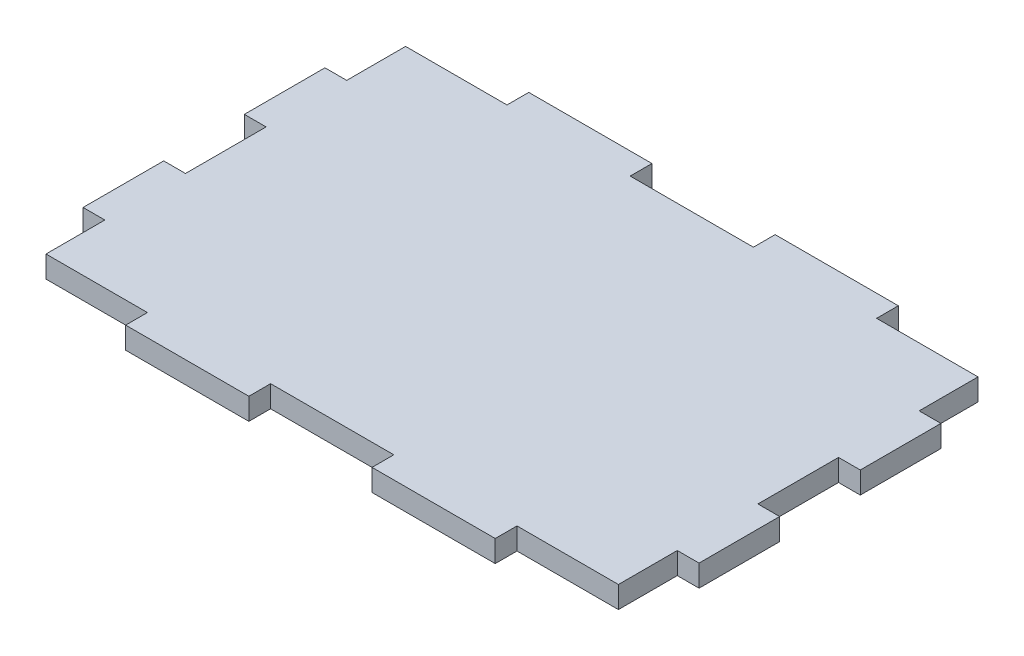
SolidWorks part; units mm, degrees
ref_plane "Ön Düzlem" through (0, 0, 0) normal (0, 0, 1) x (1, 0, 0)
ref_plane "Üst Düzlem" through (0, 0, 0) normal (0, 1, 0) x (1, 0, 0)
ref_plane "Sağ Düzlem" through (0, 0, 0) normal (1, 0, 0) x (0, 0, -1)
sketch "Sketch1" plane through (0, 0, 0) normal (0, 1, 0) x (1, 0, 0)
  line L0 (-22.92, 22.3) -> (-35.5, 22.3)
  line L2 (38.2, -15) -> (38.2, -5)
  line L3 (22.92, 25) -> (7.64, 25)
  line L5 (7.64, 22.3) -> (-7.64, 22.3)
  line L6 (35.5, 15) -> (35.5, 22.3)
  line L7 (-35.5, 22.3) -> (-35.5, 15)
  line L8 (7.64, -22.3) -> (-7.64, -22.3)
  line L9 (35.5, -22.3) -> (22.92, -22.3)
  line L10 (-38.2, -15) -> (-38.2, -5)
  line L12 (-38.2, 5) -> (-38.2, 15)
  line L14 (22.92, -25) -> (7.64, -25)
  line L16 (-7.64, -25) -> (-22.92, -25)
  line L18 (-22.92, -22.3) -> (-35.5, -22.3)
  line L19 (35.5, -5) -> (35.5, 5)
  line L20 (-35.5, 5) -> (-35.5, -5)
  line L21 (35.5, 22.3) -> (22.92, 22.3)
  line L22 (-38.2, 15) -> (-35.5, 15)
  line L23 (-38.2, 5) -> (-35.5, 5)
  line L24 (-38.2, -5) -> (-35.5, -5)
  line L25 (-38.2, -15) -> (-35.5, -15)
  line L26 (22.92, -25) -> (22.92, -22.3)
  line L27 (7.64, -25) -> (7.64, -22.3)
  line L28 (-7.64, -25) -> (-7.64, -22.3)
  line L29 (-22.92, -25) -> (-22.92, -22.3)
  line L30 (-35.5, -15) -> (-35.5, -22.3)
  line L31 (35.5, 15) -> (38.2, 15)
  line L32 (35.5, 5) -> (38.2, 5)
  line L33 (35.5, -5) -> (38.2, -5)
  line L34 (38.2, 5) -> (38.2, 15)
  line L35 (-7.64, 25) -> (-22.92, 25)
  line L36 (-22.92, 22.3) -> (-22.92, 25)
  line L37 (-7.64, 22.3) -> (-7.64, 25)
  line L38 (7.64, 22.3) -> (7.64, 25)
  line L39 (7.64, 5) -> (0, 0) construction
  line L40 (22.92, 22.3) -> (22.92, 25)
  line L41 (35.5, -15) -> (35.5, -22.3)
  line L44 (35.5, -15) -> (38.2, -15)
  point P0 (0, 0)
extrude "Boss-Extrude1" add sketch "Sketch1" against normal blind 2.7
